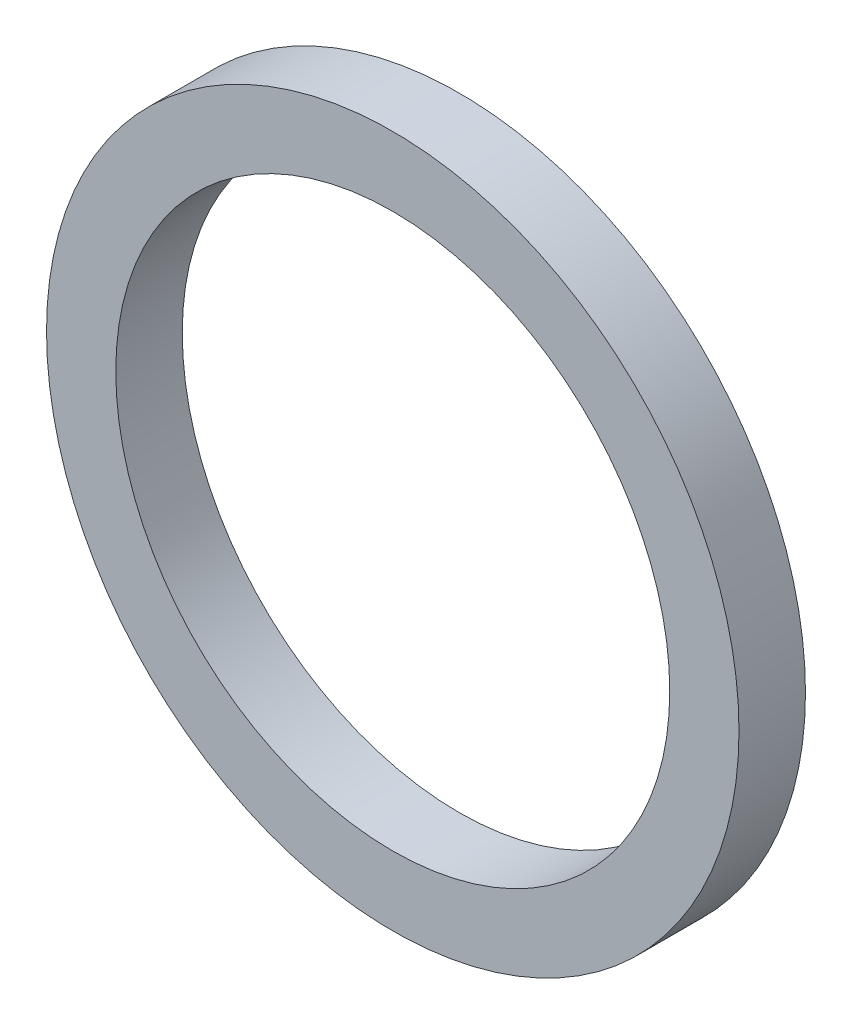
SolidWorks part; units mm, degrees
ref_plane "Alzado" through (0, 0, 0) normal (0, 0, 1) x (1, 0, 0)
ref_plane "Planta" through (0, 0, 0) normal (0, 1, 0) x (1, 0, 0)
ref_plane "Vista lateral" through (0, 0, 0) normal (1, 0, 0) x (0, 0, -1)
sketch "Sketch1" plane through (0, 0, 0) normal (0, 0, 1) x (1, 0, 0)
  circle A0 centre (0, 0) radius 3.175
  circle A1 centre (0, 0) radius 3.9688
  dimension "D1" = 6.35
  dimension "D2" = 7.9375
extrude "Boss-Extrude1" add sketch "Sketch1" along normal mid plane 0.762
